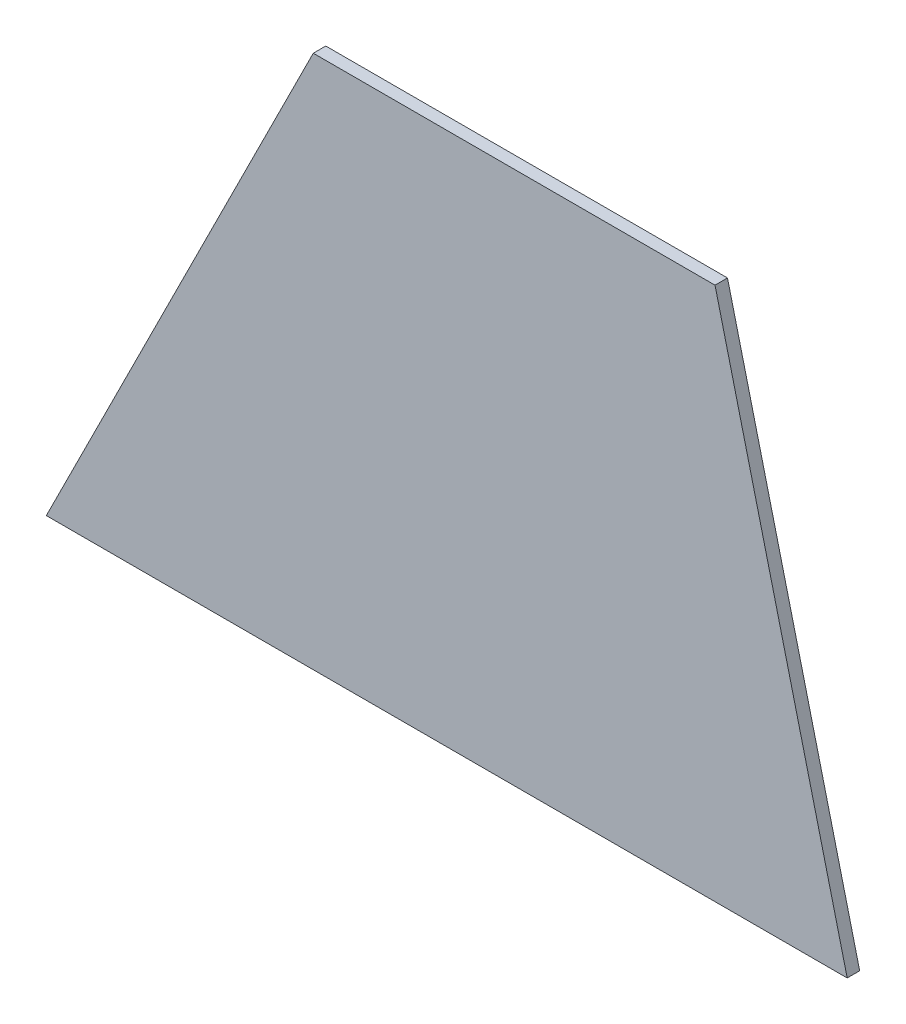
SolidWorks part; units mm, degrees
ref_plane "Front Plane" through (0, 0, 0) normal (0, 0, 1) x (1, 0, 0)
ref_plane "Top Plane" through (0, 0, 0) normal (0, 1, 0) x (1, 0, 0)
ref_plane "Right Plane" through (0, 0, 0) normal (1, 0, 0) x (0, 0, -1)
sketch "Sketch1" plane through (0, 0, 0) normal (0, 0, 1) x (1, 0, 0)
  line L1 (-217.7143, -58.0571) -> (87.0857, -58.0571)
  line L3 (-116.1143, 145.1429) -> (36.7777, 145.1429)
  line L6 (-217.7143, -58.0571) -> (-116.1143, 145.1429)
  line L7 (36.7777, 145.1429) -> (87.0857, -58.0571)
  dimension "D2" = 304.8
extrude "Boss-Extrude1" add sketch "Sketch1" along normal blind 4.7498
